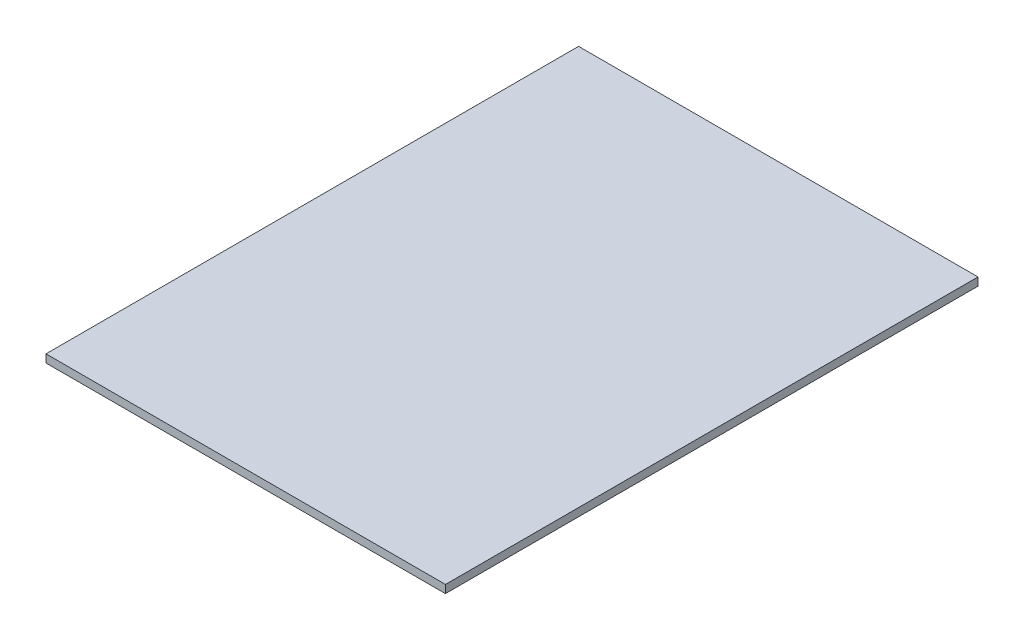
SolidWorks part; units mm, degrees
ref_plane "Front Plane" through (0, 0, 0) normal (0, 0, 1) x (1, 0, 0)
ref_plane "Top Plane" through (0, 0, 0) normal (0, 1, 0) x (1, 0, 0)
ref_plane "Right Plane" through (0, 0, 0) normal (1, 0, 0) x (0, 0, -1)
sketch "Sketch5" plane through (0, 0, 0) normal (0, 1, 0) x (1, 0, 0)
  line L1 (-75, 100) -> (75, 100)
  line L2 (-75, 100) -> (-75, -100)
  line L3 (-75, -100) -> (75, -100)
  line L4 (75, 100) -> (75, -100)
  line L5 (-75, 100) -> (75, -100) construction
  line L6 (-75, -100) -> (75, 100) construction
  point P0 (0, 0)
  dimension "D1" = 150
  dimension "D2" = 200
extrude "Boss-Extrude1" add sketch "Sketch5" along normal blind 3
